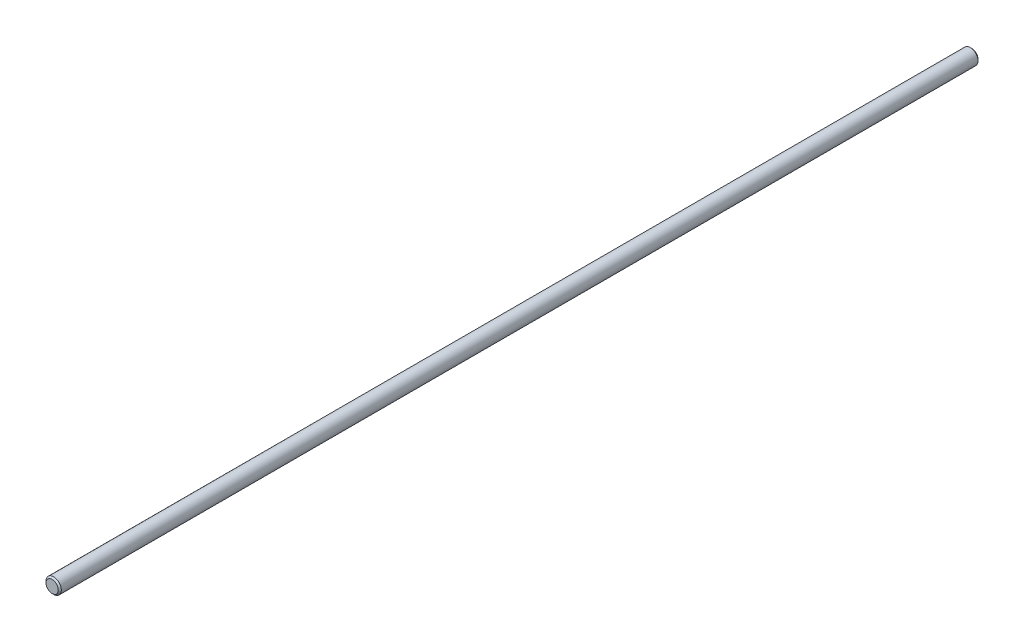
SolidWorks part; units mm, degrees
ref_plane "Front" through (0, 0, 0) normal (0, 0, 1) x (1, 0, 0)
ref_plane "Top" through (0, 0, 0) normal (0, 1, 0) x (1, 0, 0)
ref_plane "Right" through (0, 0, 0) normal (1, 0, 0) x (0, 0, -1)
sketch "Sketch1" plane through (0, 0, 0) normal (0, 0, 1) x (1, 0, 0)
  circle A0 centre (0, 0) radius 10
  dimension "D1" = 20
extrude "Extrude1" add sketch "Sketch1" along normal mid plane 1200
chamfer "Chamfer1" distance 2 angle 45 2 edges at (10, 0, -600) (10, 0, 600)
equation "\"D1@Chamfer1\" = \"D1@Sketch1\" * .1"
